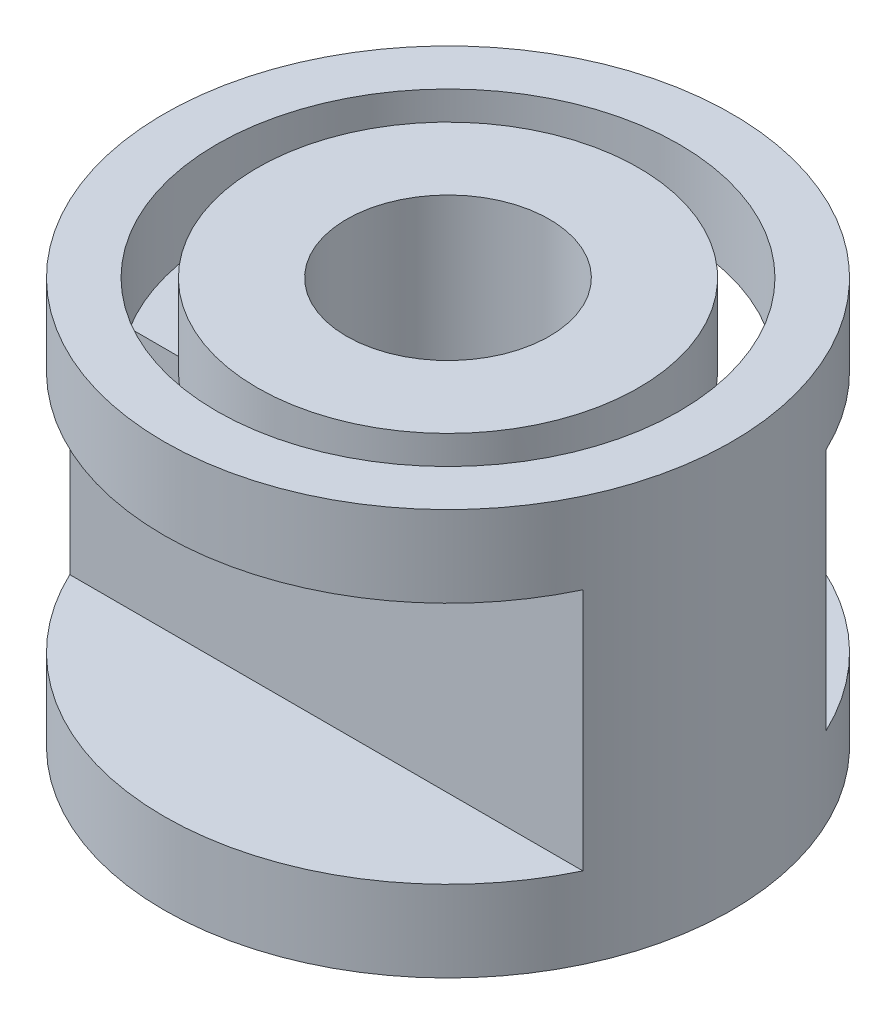
SolidWorks part; units mm, degrees
ref_plane "Plan de face" through (0, 0, 0) normal (0, 0, 1) x (1, 0, 0)
ref_plane "Plan de dessus" through (0, 0, 0) normal (0, 1, 0) x (1, 0, 0)
ref_plane "Plan de droite" through (0, 0, 0) normal (1, 0, 0) x (0, 0, -1)
sketch "Esquisse1" plane through (0, 0, 0) normal (0, 1, 0) x (1, 0, 0)
  circle A0 centre (0, 0) radius 3.5
  dimension "D1" = 7
extrude "Boss.-Extru.1" add sketch "Esquisse1" along normal blind 5
sketch "Esquisse2" plane through (0, 5, 0) normal (0, 1, 0) x (1, 0, 0)
  circle A0 centre (0, 0) radius 2.85
  circle A1 centre (0, 0) radius 2.35
  dimension "D1" = 5.7
  dimension "D2" = 0.5
extrude "Enlèv. mat.-Extru.1" cut sketch "Esquisse2" against normal blind 1
sketch "Esquisse3" plane through (0, 5, 0) normal (0, 1, 0) x (1, 0, 0)
  circle A0 centre (0, 0) radius 1.25
  dimension "D1" = 2.5
extrude "Enlèv. mat.-Extru.2" cut sketch "Esquisse3" against normal through all
sketch "Esquisse4" plane through (0, 0, 0) normal (1, 0, 0) x (0, 0, -1)
  line L4 (3.5, 0) -> (3.5, 5) construction
  line L5 (-3.5, 5) -> (-3.5, 0) construction
  line L6 (-3.5, 1) -> (-1.5, 1)
  line L7 (-3.5, 1) -> (-3.5, 4)
  line L8 (-3.5, 4) -> (-1.5, 4)
  line L9 (1.5, 4) -> (3.5, 4)
  line L10 (1.5, 4) -> (1.5, 1)
  line L11 (1.5, 1) -> (3.5, 1)
  line L12 (3.5, 4) -> (3.5, 1)
  line L13 (-1.5, 1) -> (-1.5, 4)
  line L15 (-3.5, 0) -> (3.5, 0) construction
  dimension "D3" = 3
  dimension "D4" = 3
  dimension "D5" = 2
  dimension "D6" = 2
  dimension "D7" = 1
  dimension "D8" = 1
extrude "Enlèv. mat.-Extru.3" cut sketch "Esquisse4" against normal through all both and the other way through all
